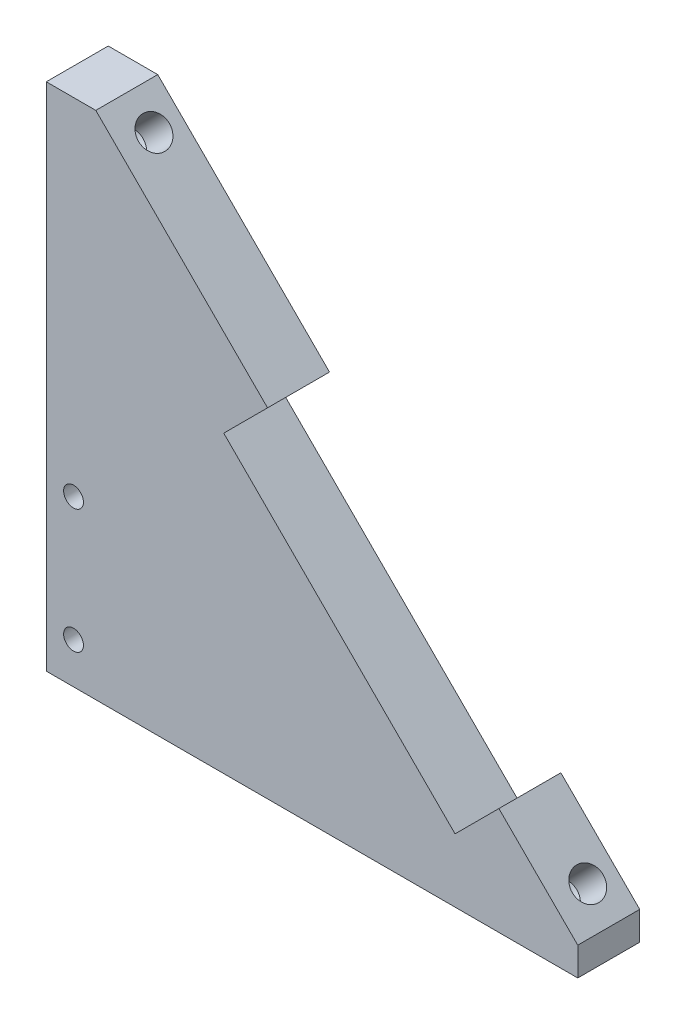
SolidWorks part; units mm, degrees
material "A286 Iron Base Superalloy"
ref_plane "Front Plane" through (0, 0, 0) normal (0, 0, 1) x (1, 0, 0)
ref_plane "Top Plane" through (0, 0, 0) normal (0, 1, 0) x (1, 0, 0)
ref_plane "Right Plane" through (0, 0, 0) normal (1, 0, 0) x (0, 0, -1)
sketch "Sketch2" plane through (0, 0, 0) normal (0, 0, 1) x (1, 0, 0)
  line L0 (-19.4454, 19.4454) -> (26.5165, -26.5165)
  line L1 (-19.4454, -26.5165) -> (26.5165, -26.5165)
  line L2 (-19.4454, -26.5165) -> (-19.4454, 19.4454)
  line L6 (-19.4454, 19.4454) -> (26.5165, -26.5165) construction
  point P0 (0, 0)
  dimension "D1" = 65
  dimension "D2" = 45
  dimension "D3" = 45.9619
  dimension "D4" = 45.9619
extrude "Boss-Extrude1" add sketch "Sketch2" along normal blind 5
sketch "Sketch3" plane through (0, 0, 0) normal (0.7071, 0.7071, 0) x (0, 0, -1)
  line L0 (-5, -37.5) -> (-5, 27.5) construction
  line L4 (-5, 27.5) -> (0, 27.5) construction
  circle A0 centre (-2.25, -29.75) radius 1.5
  circle A1 centre (-2.25, 19.75) radius 1.5
  dimension "D3" = 3
  dimension "D4" = 3
  dimension "D1" = 2.75
  dimension "D2" = 7.75
  dimension "D5" = 2.75
hole_wizard "M3x0.5 Tapped Hole1" positions "Sketch5" profile "Sketch4" tap size "M3x0.5" standard "ANSI Metric"
sketch "Sketch5" plane through (0, 0, 0) normal (0.7071, 0.7071, 0) x (0, 0, -1)
  point P0 (-2.25, 19.75)
  point P3 (-2.25, -29.75)
sketch "Sketch4" plane through (-13.9654, 13.9654, 2.25) normal (0, 0, 1) x (-0.7071, 0.7071, 0)
  line L0 (0, 0) -> (0, 3.7511)
  line L1 (0, 3.7511) -> (1.25, 3)
  line L2 (1.25, 3) -> (1.25, 0)
  line L5 (1.25, 0) -> (0, 0)
  line L10 (0, 3.7511) -> (-1.25, 3) construction
  line L11 (0, -6.35) -> (0, 107.95) construction
  dimension "Tap Drill Dia." = 2.5
  dimension "Tap Drill Depth" = 3
  dimension "Drill Angle" = 118
cosmetic thread "Hole Thread1" parameters "D1"=3, "D2"=3
cosmetic thread "Hole Thread2" parameters "D1"=3, "D2"=3
sketch "Sketch6" plane through (0, 0, 5) normal (0, 0, 1) x (1, 0, 0)
  line L0 (-19.4454, 19.4454) -> (-15.9099, 15.9099)
  line L1 (26.5165, -26.5165) -> (-19.4454, 19.4454) construction
  line L2 (-15.9099, 15.9099) -> (-14.4957, 17.3241)
  line L3 (-14.4957, 17.3241) -> (-18.0312, 20.8597)
  line L4 (-18.0312, 20.8597) -> (-19.4454, 19.4454)
  line L5 (26.5165, -26.5165) -> (22.981, -22.981)
  line L6 (22.981, -22.981) -> (24.3952, -21.5668)
  line L7 (24.3952, -21.5668) -> (27.9307, -25.1023)
  line L8 (27.9307, -25.1023) -> (26.5165, -26.5165)
  dimension "D1" = 2
  dimension "D2" = 5
  dimension "D3" = 2
  dimension "D4" = 5
extrude "Boss-Extrude2" add sketch "Sketch6" against normal through all
sketch "Sketch7" plane through (0, 0, 5) normal (0, 0, 1) x (1, 0, 0)
  line L0 (-2.0506, 2.0506) -> (-5.5861, -1.4849)
  line L1 (22.981, -22.981) -> (-15.9099, 15.9099) construction
  line L2 (-5.5861, -1.4849) -> (13.0815, -20.1525)
  line L3 (13.0815, -20.1525) -> (16.617, -16.617)
  line L4 (16.617, -16.617) -> (-2.0506, 2.0506)
  line L5 (-18.0312, 20.8597) -> (-19.4454, 19.4454) construction
  line L7 (26.5165, -26.5165) -> (27.9307, -25.1023) construction
  dimension "D1" = 5
  dimension "D2" = 24.6
  dimension "D3" = 14
extrude "Cut-Extrude1" cut sketch "Sketch7" against normal through all
sketch "Sketch8" plane through (0, 0, 5) normal (0, 0, 1) x (1, 0, 0)
  line L0 (-18.0312, 20.8597) -> (-14.4957, 17.3241)
  line L1 (-14.4957, 17.3241) -> (-15.9099, 15.9099)
  line L2 (-15.9099, 15.9099) -> (-2.0506, 2.0506)
  line L3 (-2.0506, 2.0506) -> (-5.5861, -1.4849)
  line L4 (-5.5861, -1.4849) -> (13.0815, -20.1525)
  line L5 (13.0815, -20.1525) -> (16.617, -16.617)
  line L6 (16.617, -16.617) -> (22.981, -22.981)
  line L7 (22.981, -22.981) -> (24.3952, -21.5668)
  line L8 (24.3952, -21.5668) -> (27.9307, -25.1023)
  line L9 (27.9307, -25.1023) -> (26.5165, -26.5165)
  line L10 (26.5165, -26.5165) -> (-19.4454, -26.5165)
  line L11 (-19.4454, -26.5165) -> (-19.4454, 19.4454)
  line L12 (-19.4454, 19.4454) -> (-18.0312, 20.8597)
sketch "Sketch9" plane through (0, 0, 5) normal (0, 0, 1) x (1, 0, 0)
  line L0 (-15.9099, 15.9099) -> (-19.4454, 12.3744)
  line L1 (-19.4454, 19.4454) -> (-19.4454, -26.5165) construction
  line L2 (-19.4454, 12.3744) -> (-19.4454, 19.4454)
  line L3 (-19.4454, 19.4454) -> (-18.0312, 20.8597)
  line L4 (-14.4957, 17.3241) -> (-18.0312, 20.8597) construction
  line L5 (-18.0312, 20.8597) -> (-19.4454, 19.4454) construction
  line L6 (-18.0312, 20.8597) -> (-14.4957, 17.3241)
  line L7 (-14.4957, 17.3241) -> (-15.9099, 15.9099)
  line L8 (27.9307, -25.1023) -> (24.3952, -21.5668)
  line L9 (24.3952, -21.5668) -> (19.4454, -26.5165)
  line L10 (-19.4454, -26.5165) -> (26.5165, -26.5165) construction
  line L11 (19.4454, -26.5165) -> (26.5165, -26.5165)
  line L12 (26.5165, -26.5165) -> (27.9307, -25.1023)
extrude "Cut-Extrude2" cut sketch "Sketch9" against normal through all
sketch "Sketch13" plane through (0, 0, 5) normal (0, 0, 1) x (1, 0, 0)
  line L0 (22.981, -22.981) -> (19.4454, -26.5165)
  line L1 (19.4454, -26.5165) -> (22.981, -26.5165)
  line L2 (22.981, -22.981) -> (22.981, -26.5165)
extrude "Boss-Extrude3" add sketch "Sketch13" against normal through all
sketch "Sketch14" plane through (0, 0, 5) normal (0, 0, 1) x (1, 0, 0)
  line L0 (-19.4454, 12.3744) -> (-19.4454, 15.9099)
  line L1 (-19.4454, 15.9099) -> (-15.9099, 15.9099)
  line L2 (-15.9099, 15.9099) -> (-19.4454, 12.3744)
extrude "Boss-Extrude4" add sketch "Sketch14" against normal through all
sketch "Sketch15" plane through (0, 0, 0) normal (0, 0, -1) x (-1, 0, 0)
  line L1 (19.4454, -26.5165) -> (-22.981, -26.5165)
  line L2 (19.4454, -26.5165) -> (19.4454, -26.9765)
  line L3 (19.4454, -26.9765) -> (-22.981, -26.9765)
  line L4 (-22.981, -26.5165) -> (-22.981, -26.9765)
  line L5 (19.4454, -26.5165) -> (19.9054, -26.5165)
  line L6 (19.4454, -26.5165) -> (19.4454, 15.9099)
  line L7 (19.4454, 15.9099) -> (19.9054, 15.9099)
  line L8 (19.9054, -26.5165) -> (19.9054, 15.9099)
  line M3 (-22.981, -26.5165) -> (19.4454, -26.5165)
  dimension "D1" = 0.46
  dimension "D2" = 0.46
extrude "Boss-Extrude6" add sketch "Sketch15" against normal through all contours L4 L3 L2 M3
sketch "Sketch16" plane through (0, 0, 0) normal (0, 0, -1) x (-1, 0, 0)
  line L1 (19.4454, 15.9099) -> (19.9054, 15.9099)
  line L2 (19.4454, 15.9099) -> (19.4454, -26.9765)
  line L3 (19.4454, -26.9765) -> (19.9054, -26.9765)
  line L4 (19.9054, 15.9099) -> (19.9054, -26.9765)
  dimension "D1" = 0.46
extrude "Boss-Extrude7" add sketch "Sketch16" against normal through all
sketch "Sketch17" plane through (0, 0, 0) normal (0, 0, -1) x (-1, 0, 0)
  line L1 (19.9054, -26.9765) -> (-22.981, -26.9765) construction
  circle A0 centre (17.7062, -11.9765) radius 1.5
  circle A1 centre (17.7062, -21.9765) radius 1.5
  dimension "D1" = 3
  dimension "D2" = 3
  dimension "D3" = 5
  dimension "D4" = 10
hole_wizard "M2x0.4 Tapped Hole1" positions "Sketch19" profile "Sketch18" tap size "M2x0.4" standard "ANSI Metric"
sketch "Sketch19" plane through (0, 0, 0) normal (0, 0, -1) x (-1, 0, 0)
  point P0 (17.7062, -11.9765)
  point P3 (17.7062, -21.9765)
sketch "Sketch18" plane through (-17.7062, -11.9765, 0) normal (1, 0, 0) x (0, 1, 0)
  line L0 (0, 0) -> (0, 6.4807)
  line L1 (0, 6.4807) -> (0.8, 6)
  line L2 (0.8, 6) -> (0.8, 0)
  line L5 (0.8, 0) -> (0, 0)
  line L10 (0, 6.4807) -> (-0.8, 6) construction
  line L11 (0, -6.35) -> (0, 107.95) construction
  dimension "Tap Drill Dia." = 1.6
  dimension "Tap Drill Depth" = 6
  dimension "Drill Angle" = 118
cosmetic thread "Hole Thread3" parameters "D1"=4, "D2"=2
cosmetic thread "Hole Thread4" parameters "D1"=4, "D2"=2
sketch "Sketch20" plane through (0, 0, 5) normal (0, 0, 1) x (1, 0, 0)
  line L0 (-19.9054, -26.9765) -> (22.981, -26.9765) construction
  line L1 (22.981, -26.9765) -> (22.981, -22.981) construction
  circle A0 centre (-10.469, -24.9765) radius 1.5
  circle A1 centre (9.531, -24.9765) radius 1.5
  point P6 (22.981, -24.9787)
  dimension "D1" = 3
  dimension "D2" = 3
  dimension "D3" = 2
  dimension "D4" = 2
  dimension "D5" = 13.45
  dimension "D6" = 20
sketch "Sketch21" plane through (0, 0, 5) normal (0, 0, 1) x (1, 0, 0)
  line L0 (-19.9054, -26.9765) -> (-19.9054, 15.9099) construction
  line L1 (22.981, -26.9765) -> (-19.9054, -26.9765)
  line L2 (22.981, -26.9765) -> (22.981, -25.2765)
  line L3 (22.981, -25.2765) -> (-19.9054, -25.2765)
  line L4 (-19.9054, -26.9765) -> (-19.9054, -25.2765)
  dimension "D1" = 1.7
extrude "Cut-Extrude3" cut sketch "Sketch21" against normal through all
sketch "Sketch22" plane through (0, -25.2765, 0) normal (0, -1, 0) x (1, 0, 0)
  line L0 (-19.9054, 0) -> (-19.9054, 5) construction
  line L1 (22.981, 5) -> (-19.9054, 5) construction
  circle A0 centre (-7.9054, 2.5) radius 1.5
  circle A1 centre (7.0946, 2.5) radius 1.5
  dimension "D1" = 3
  dimension "D2" = 3
  dimension "D3" = 15
  dimension "D4" = 12
  dimension "D5" = 2.5
hole_wizard "M3x0.5 Tapped Hole3" positions "Sketch24" profile "Sketch23" tap size "M3x0.5" standard "ANSI Metric"
sketch "Sketch24" plane through (0, -25.2765, 0) normal (0, -1, 0) x (-1, 0, 0)
  point P0 (7.9054, -2.5)
  point P3 (-7.0946, -2.5)
sketch "Sketch23" plane through (-7.9054, -25.2765, 2.5) normal (1, 0, 0) x (0, 0, -1)
  line L0 (0, 0) -> (0, 6.7511)
  line L1 (0, 6.7511) -> (1.25, 6)
  line L2 (1.25, 6) -> (1.25, 0)
  line L5 (1.25, 0) -> (0, 0)
  line L10 (0, 6.7511) -> (-1.25, 6) construction
  line L11 (0, -6.35) -> (0, 107.95) construction
  dimension "Tap Drill Dia." = 2.5
  dimension "Tap Drill Depth" = 6
  dimension "Drill Angle" = 118
cosmetic thread "Hole Thread5" parameters "D1"=6, "D2"=3
cosmetic thread "Hole Thread6" parameters "D1"=6, "D2"=3
